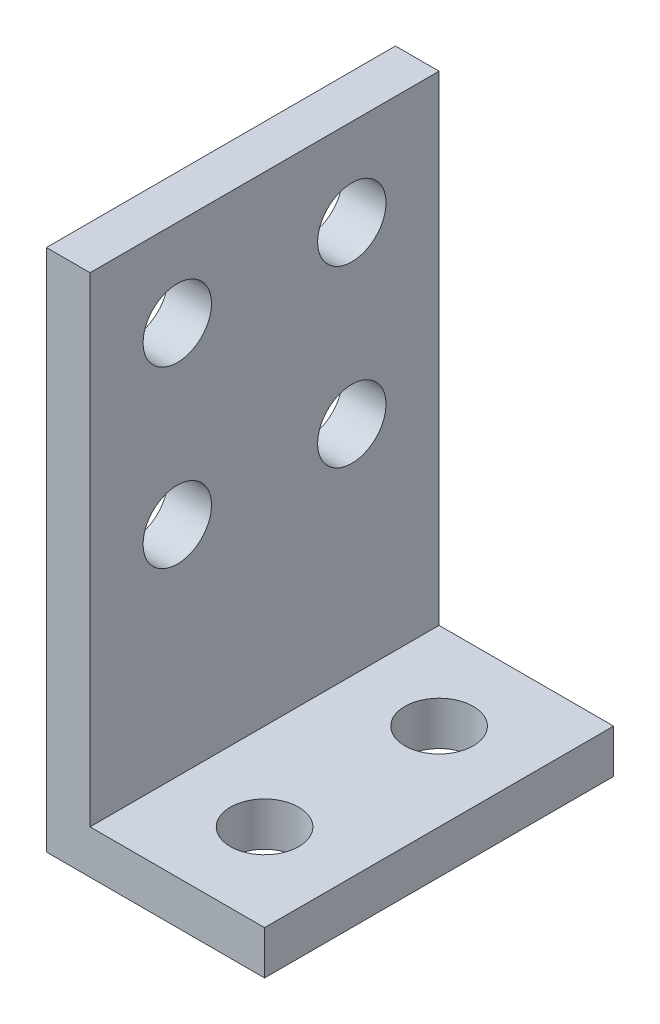
SolidWorks part; units mm, degrees
material "6061-T6 (SS)"
ref_plane "Front Plane" through (0, 0, 0) normal (0, 0, 1) x (1, 0, 0)
ref_plane "Top Plane" through (0, 0, 0) normal (0, 1, 0) x (1, 0, 0)
ref_plane "Right Plane" through (0, 0, 0) normal (1, 0, 0) x (0, 0, -1)
sketch "Sketch1" plane through (0, 0, 0) normal (0, 0, 1) x (1, 0, 0)
  line L0 (0, 0) -> (0, 38.1)
  line L1 (0, 38.1) -> (3.175, 38.1)
  line L2 (3.175, 38.1) -> (3.175, 3.175)
  line L3 (3.175, 3.175) -> (15.875, 3.175)
  line L4 (15.875, 3.175) -> (15.875, 0)
  line L5 (15.875, 0) -> (0, 0)
  dimension "D1" = 3.175
  dimension "D2" = 38.1
  dimension "D3" = 15.875
extrude "Boss-Extrude1" add sketch "Sketch1" along normal blind 25.4
sketch "Sketch2" plane through (0, 3.175, 0) normal (0, 1, 0) x (1, 0, 0)
  line L0 (15.875, -25.4) -> (3.175, -25.4) construction
  line L1 (3.175, -25.4) -> (3.175, 0) construction
  circle A0 centre (9.525, -6.35) radius 2.4892
  circle A1 centre (9.525, -19.05) radius 2.4892
  dimension "D1" = 4.9784
  dimension "D2" = 12.7
  dimension "D3" = 6.35
  dimension "D4" = 6.35
extrude "Cut-Extrude1" cut sketch "Sketch2" against normal through all
sketch "Sketch4" plane through (0, 0, 0) normal (-1, 0, 0) x (0, 0, 1)
  line L0 (0, 38.1) -> (0, 0) construction
  line L5 (25.4, 0) -> (0, 0) construction
  circle A0 centre (6.35, 31.75) radius 2.4892
  circle A1 centre (19.05, 31.75) radius 2.4892
  circle A2 centre (19.05, 19.05) radius 2.4892
  circle A3 centre (6.35, 19.05) radius 2.4892
  dimension "D5" = 6.35
  dimension "D6" = 19.05
  dimension "D7" = 4.9784
  dimension "D3" = 12.7
  dimension "D4" = 12.7
  dimension "D1" = 2
  dimension "D2" = 2
extrude "Cut-Extrude2" cut sketch "Sketch4" against normal through all
